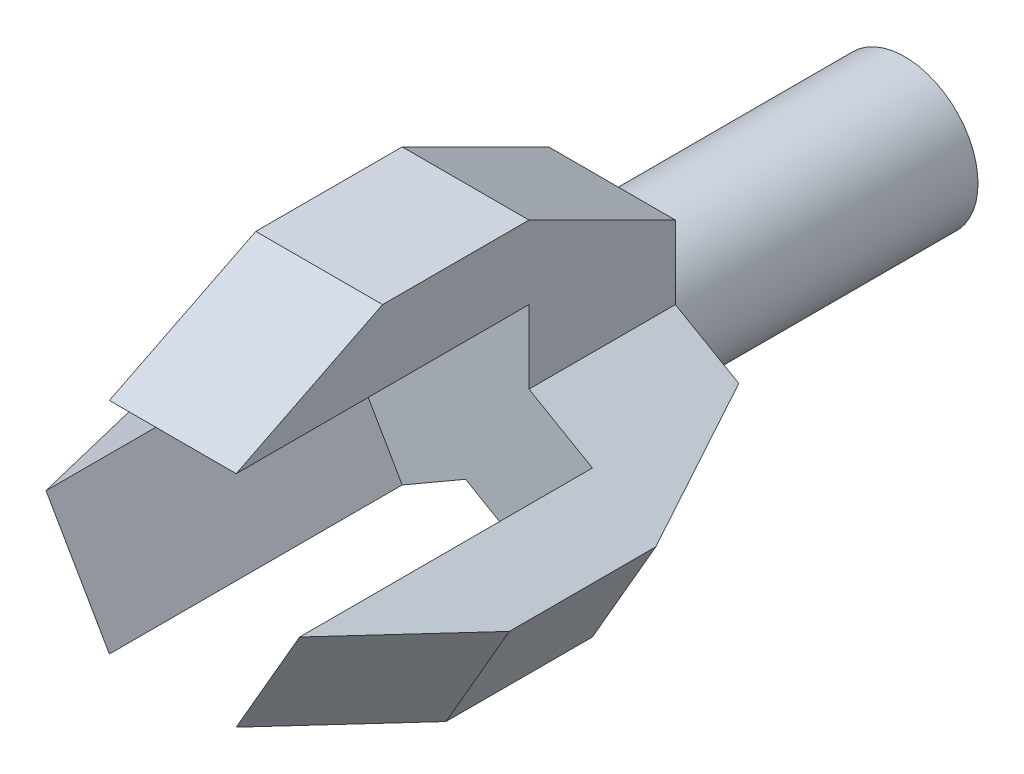
SolidWorks part; units mm, degrees
material "Brass"
ref_plane "Front Plane" through (0, 0, 0) normal (0, 0, 1) x (1, 0, 0)
ref_plane "Top Plane" through (0, 0, 0) normal (0, 1, 0) x (1, 0, 0)
ref_plane "Right Plane" through (0, 0, 0) normal (1, 0, 0) x (0, 0, -1)
sketch "Sketch1" plane through (0, 0, 0) normal (0, 0, 1) x (1, 0, 0)
  circle A0 centre (0, 0) radius 50
  dimension "D1" = 100
extrude "Boss-Extrude1" add sketch "Sketch1" along normal blind 200
sketch "Sketch2" plane through (0, 0, 200) normal (0, 0, 1) x (1, 0, 0)
  line L0 (43.3013, 25) -> (43.3013, 75)
  line L1 (0, 0) -> (0, 227.9839) construction
  line L3 (-43.3013, 25) -> (43.3013, 25) construction
  line L4 (43.3013, 75) -> (-43.3013, 75)
  line L5 (-43.3013, 75) -> (-43.3013, 25)
  line L12 (-43.3013, 25) -> (0, 0)
  line L13 (0, 0) -> (43.3013, 25)
  circle A1 centre (0, 0) radius 50 construction
  point P3 (0, 75)
  dimension "D1" = 60
  dimension "D2" = 120
  dimension "D3" = 75
  dimension "D4" = 25
extrude "Boss-Extrude2" add sketch "Sketch2" along normal blind 100
sketch "Sketch3" plane through (-43.3013, 0, 0) normal (-1, 0, 0) x (0, 1, 0)
  line L0 (75, -300) -> (75, -200) construction
  line L1 (75, -200) -> (75, -500)
  line L2 (75, -200) -> (125, -300)
  line L3 (125, -300) -> (125, -400)
  line L4 (125, -400) -> (75, -500)
  line L5 (75, -200) -> (25, -200) construction
  dimension "D1" = 50
  dimension "D2" = 100
  dimension "D3" = 100
  dimension "D4" = 100
extrude "Boss-Extrude4" add sketch "Sketch3" against normal up to surface (86.6025 mm away) up to face at (43.3013, 50, 250)
pattern_circular "CirPattern1" count 3 every 120 about axis through (0, 0, 0) along (0, 0, 1) of "Boss-Extrude2", "Boss-Extrude4"
